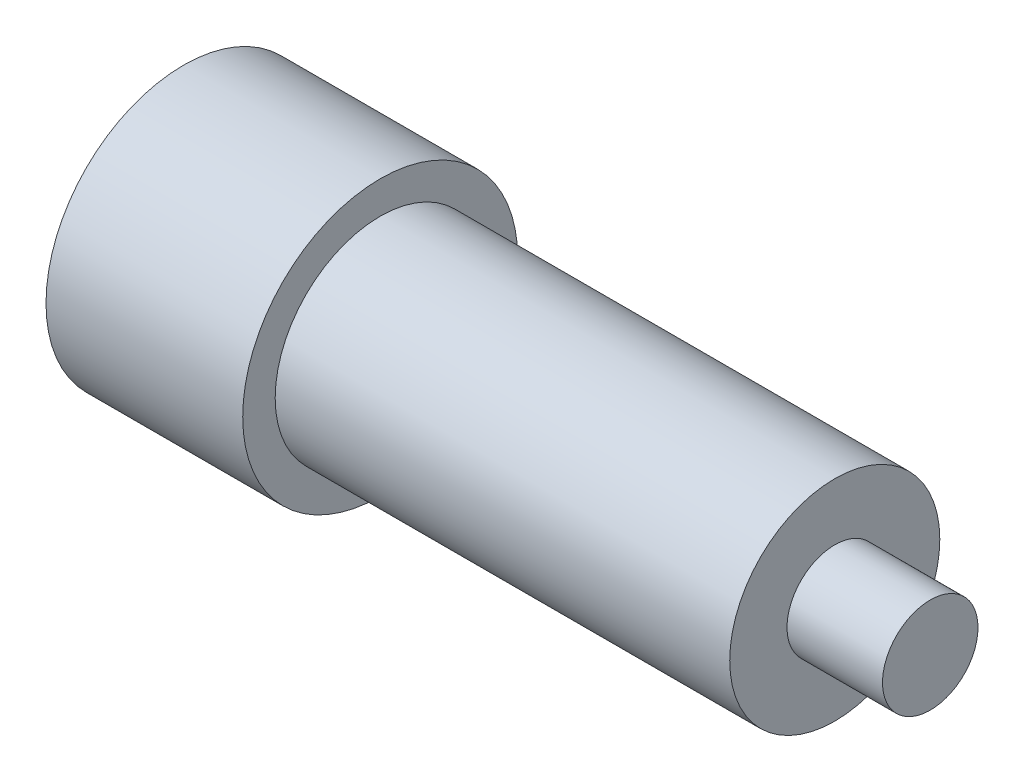
SolidWorks part; units mm, degrees
ref_plane "Front Plane" through (0, 0, 0) normal (0, 0, 1) x (1, 0, 0)
ref_plane "Top Plane" through (0, 0, 0) normal (0, 1, 0) x (1, 0, 0)
ref_plane "Right Plane" through (0, 0, 0) normal (1, 0, 0) x (0, 0, -1)
sketch "Sketch1" plane through (0, 0, 0) normal (1, 0, 0) x (0, 0, -1)
  circle A0 centre (0, 0) radius 5.5
  point P0 (0, 0)
  dimension "D1" = 11
extrude "Boss-Extrude2" add sketch "Sketch1" along normal blind 23.8
sketch "Sketch2" plane through (0, 0, 0) normal (-1, 0, 0) x (0, 0, 1)
  circle A0 centre (0, 0) radius 7.2
  point P0 (0, 0)
  point P4 (-12.4249, -6.4017)
extrude "Boss-Extrude4" add sketch "Sketch2" along normal blind 10.3 contours A0
sketch "Sketch3" plane through (23.8, 0, 0) normal (1, 0, 0) x (0, 0, -1)
  circle A0 centre (0, 0) radius 2.5
  point P0 (0, 0)
extrude "Boss-Extrude5" add sketch "Sketch3" along normal blind 5
